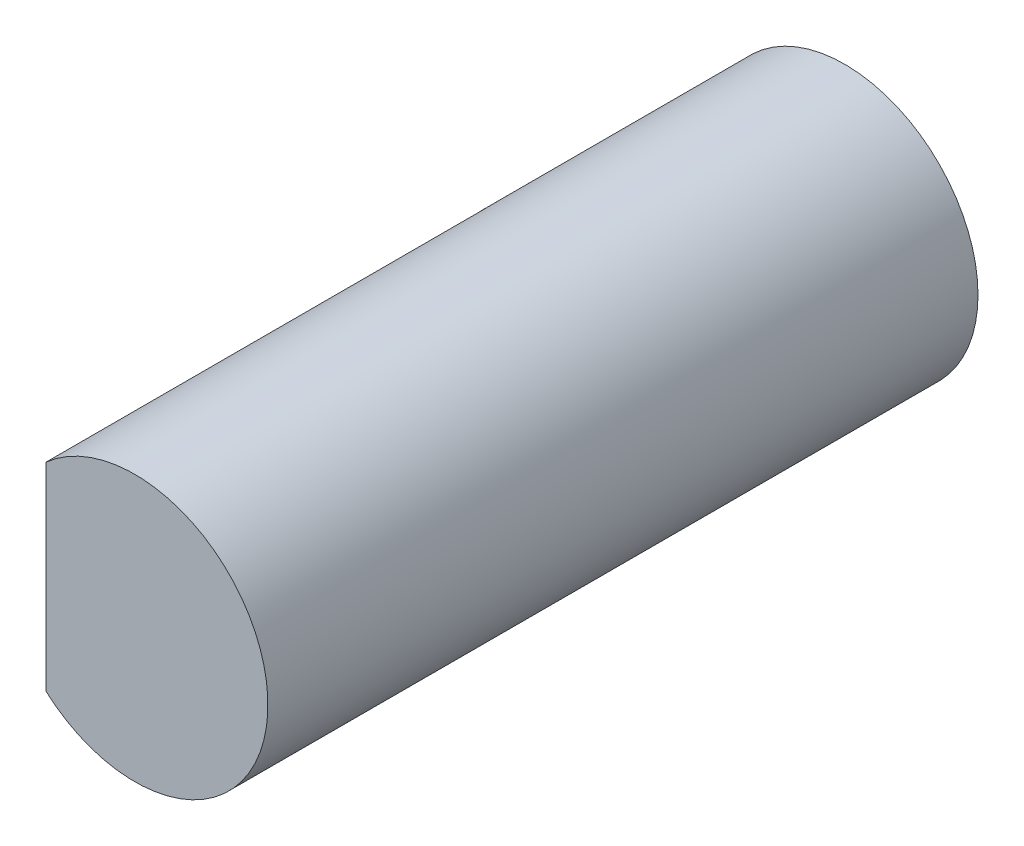
SolidWorks part; units mm, degrees
ref_plane "Front Plane" through (0, 0, 0) normal (0, 0, 1) x (1, 0, 0)
ref_plane "Top Plane" through (0, 0, 0) normal (0, 1, 0) x (1, 0, 0)
ref_plane "Right Plane" through (0, 0, 0) normal (1, 0, 0) x (0, 0, -1)
sketch "Sketch1" plane through (0, 0, 0) normal (0, 0, 1) x (1, 0, 0)
  circle A0 centre (0, 0) radius 1.5
  dimension "D1" = 3
extrude "Boss-Extrude1" add sketch "Sketch1" along normal blind 8
sketch "Sketch2" plane through (0, 0, 8) normal (0, 0, 1) x (1, 0, 0)
  line L1 (-1.6, 1.5) -> (-1, 1.5)
  line L2 (-1.6, 1.5) -> (-1.6, -1.5)
  line L3 (-1.6, -1.5) -> (-1, -1.5)
  line L4 (-1, 1.5) -> (-1, -1.5)
  dimension "D1" = 1.5
  dimension "D2" = 0.6
  dimension "D3" = 3
  dimension "D4" = 1
extrude "Cut-Extrude1" cut sketch "Sketch2" against normal blind 5
